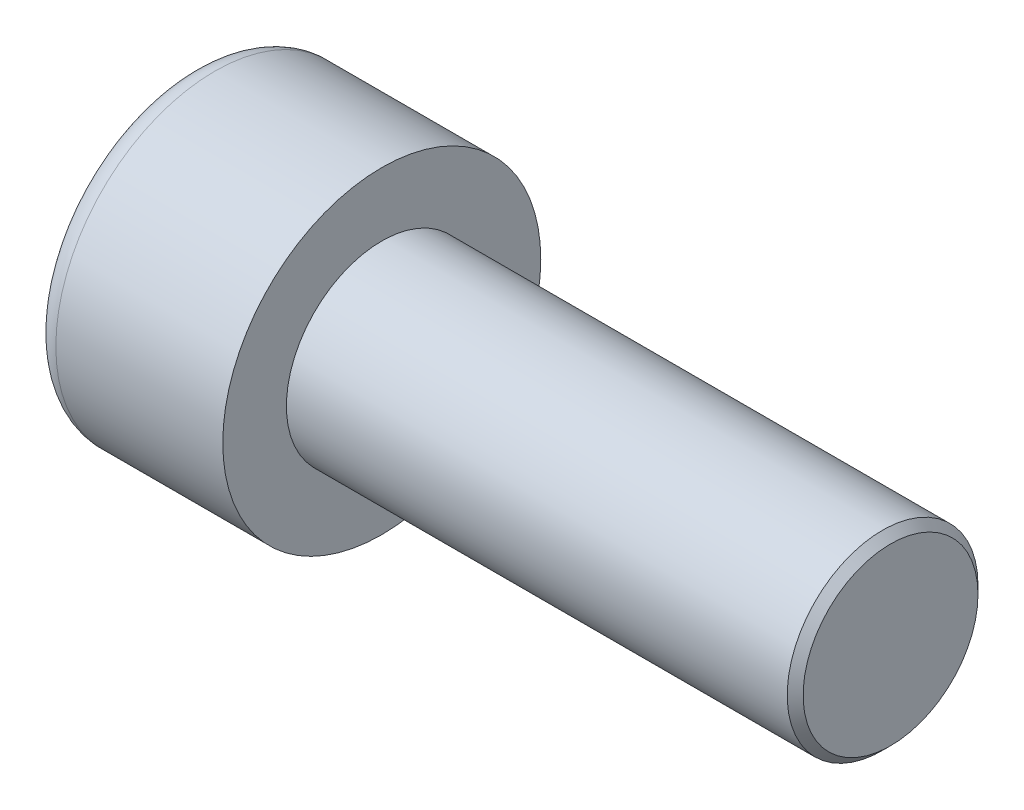
SolidWorks part; units mm, degrees
ref_plane "Front" through (0, 0, 0) normal (0, 0, 1) x (1, 0, 0)
ref_plane "Top" through (0, 0, 0) normal (0, 1, 0) x (1, 0, 0)
ref_plane "Right" through (0, 0, 0) normal (1, 0, 0) x (0, 0, -1)
sketch "Sketch1" plane through (0, 0, 0) normal (1, 0, 0) x (0, 0, -1)
  circle A0 centre (0, 0) radius 5
  dimension "dk" = 10
extrude "BaseHead" add sketch "Sketch1" along normal blind 6
sketch "Sketch2" plane through (6, 0, 0) normal (1, 0, 0) x (0, 0, -1)
  circle A0 centre (0, 0) radius 3
  dimension "d" = 6
extrude "BaseBody" add sketch "Sketch2" along normal blind 16
cosmetic thread "ThreadCosmetic1" parameters "b"=16, "D2"=4.917
sketch "Sketch3" plane through (0, 0, 0) normal (1, 0, 0) x (0, 0, -1)
  line L1 (2.8868, 0) -> (1.4434, 2.5)
  line L2 (1.4434, 2.5) -> (-1.4434, 2.5)
  line L3 (-1.4434, 2.5) -> (-2.8868, 0)
  line L4 (-2.8868, 0) -> (-1.4434, -2.5)
  line L5 (-1.4434, -2.5) -> (1.4434, -2.5)
  line L6 (1.4434, -2.5) -> (2.8868, 0)
  circle A0 centre (0, 0) radius 2.5 construction
  dimension "s" = 5
  dimension "e" = 5.7735
extrude "HexagonSocket" cut sketch "Sketch3" along normal blind 3
sketch "Sketch4" plane through (-4.1961, 0.75, 0) normal (0, 0, 1) x (-1, 0, 0)
  line L0 (-7.1961, 3.25) -> (-8.6395, 0.75)
  line L2 (-8.6395, 0.75) -> (-7.1961, 0.75)
  line L3 (-7.1961, 0.75) -> (-7.1961, 3.25)
  line L4 (-5.0351, 0.75) -> (0.839, 0.75) construction
  line L5 (-26.1961, 0.75) -> (-10.1961, 0.75) construction
  line L6 (-10.1961, 0.75) -> (-4.1961, 0.75) construction
  dimension "m" = 60
revolve "Cut-Revolve1" cut sketch "Sketch4" angle 360 about L4
fillet "HeadFillet" [suppressed] radius 0.25
fillet "TopFillet" radius 0.75 1 edges at (0, 0, -5)
chamfer "Chamfer1" distance 0.25 angle 45 1 edges at (22, 0, -3)
sketch "Sketch5" plane through (0, 0, 0) normal (0, 0, 1) x (1, 0, 0)
  line L0 (21.75, 2.531) -> (22.0207, 3)
  line L1 (22.0207, 3) -> (22.0207, 3.5415)
  line L2 (22.0207, 3.5415) -> (21.4792, 3.5415)
  line L3 (21.4792, 3.5415) -> (21.4792, 3)
  line L4 (21.4792, 3) -> (21.75, 2.531)
  line L5 (0, 0) -> (7.8886, 0) construction
  line L6 (21.75, -3) -> (21.75, 3) construction
  dimension "D1" = 6
  dimension "D2" = 0.5415
revolve "Cut-Revolve10" [suppressed] cut sketch "Sketch5" angle 360 about L5
pattern_linear "LPattern10" [suppressed] count 25 spacing 0.6498 along (1, 0, 0)
equation "\"r1@TopFillet\" = \"d@Sketch2\" / 8"
equation "\"D1@Chamfer1\" = \"r@HeadFillet\""
equation "\"D1@Sketch5\" = \"d@Sketch2\""
equation "\"D2@Sketch5\" =  ( \"d@Sketch2\" - \"D2@ThreadCosmetic1\" )  / 2"
equation "\"D3@LPattern10\" = \"D2@Sketch5\" * 1.2"
equation "\"D1@LPattern10\" = \"b@ThreadCosmetic1\" / \"D3@LPattern10\""
